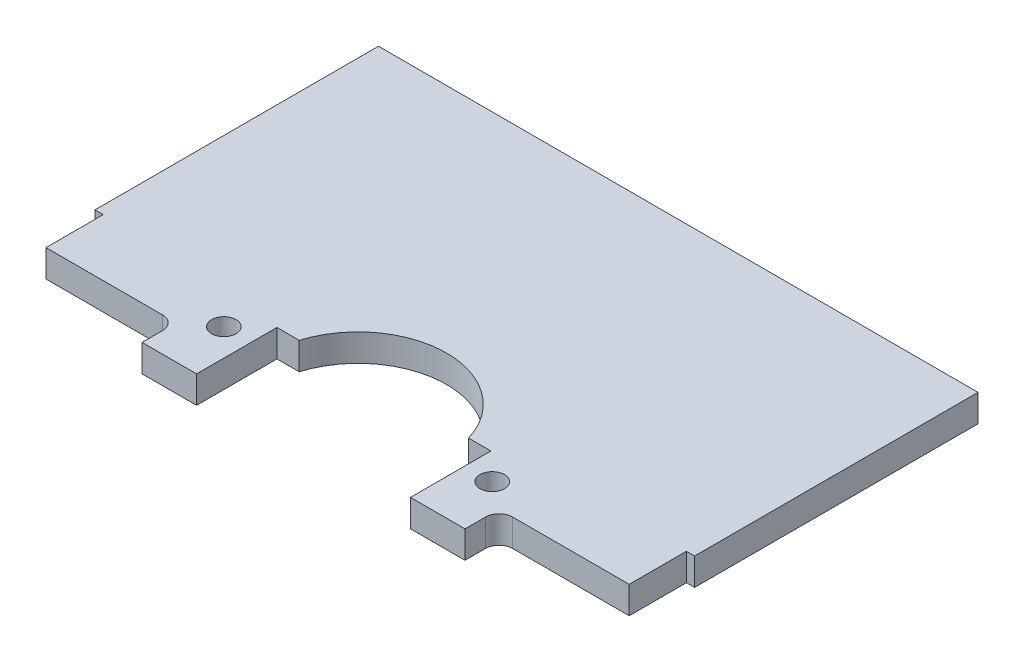
SolidWorks part; units mm, degrees
ref_plane "Front Plane" through (0, 0, 0) normal (0, 0, 1) x (1, 0, 0)
ref_plane "Top Plane" through (0, 0, 0) normal (0, 1, 0) x (1, 0, 0)
ref_plane "Right Plane" through (0, 0, 0) normal (1, 0, 0) x (0, 0, -1)
sketch "Sketch1" plane through (0, 0, 0) normal (0, 1, 0) x (1, 0, 0)
  line L0 (0, 0) -> (0, -20.1295) construction
  line L1 (-27.94, -13.208) -> (27.94, -13.208)
  line L2 (-27.94, -13.208) -> (-27.94, 13.208)
  line L3 (-27.94, 13.208) -> (27.94, 13.208)
  line L4 (27.94, -13.208) -> (27.94, 13.208)
  line L5 (-27.94, -13.208) -> (27.94, 13.208) construction
  line L6 (-27.94, 13.208) -> (27.94, -13.208) construction
  line L7 (-9.9695, -21.717) -> (-9.9695, -14.224)
  line L8 (-27.178, -18.542) -> (27.178, -18.542)
  line L9 (-27.178, -18.542) -> (-27.178, -13.208)
  line L10 (-27.178, -13.208) -> (27.178, -13.208)
  line L11 (27.178, -18.542) -> (27.178, -13.208)
  line L12 (-27.178, -18.542) -> (27.178, -13.208) construction
  line L13 (-27.178, -13.208) -> (27.178, -18.542) construction
  line L14 (-15.0495, -21.717) -> (15.0495, -21.717)
  line L15 (-15.0495, -21.717) -> (-15.0495, -18.542)
  line L16 (-15.0495, -18.542) -> (15.0495, -18.542)
  line L17 (15.0495, -21.717) -> (15.0495, -18.542)
  line L18 (-15.0495, -21.717) -> (15.0495, -18.542) construction
  line L19 (-15.0495, -18.542) -> (15.0495, -21.717) construction
  line L20 (-9.9695, -14.224) -> (9.9695, -14.224)
  line L21 (9.9695, -14.224) -> (9.9695, -21.717)
  line L22 (-12.5095, -21.717) -> (-12.5095, -16.637) construction
  line L23 (12.5095, -21.717) -> (12.5095, -16.637) construction
  line L24 (-12.5095, -16.637) -> (12.5095, -16.637) construction
  circle A0 centre (-12.5095, -16.637) radius 1.143
  circle A1 centre (12.5095, -16.637) radius 1.143
  arc A2 (-7.8945, -14.224) -> (7.8945, -14.224) centre (0, -16.637) cw
  point P0 (0, 0)
  point P8 (0, -15.875)
  dimension "D11" = 2.286
  dimension "D12" = 8.255
  dimension "D1" = 55.88
  dimension "D2" = 26.416
  dimension "D3" = 31.75
  dimension "D4" = 0.762
  dimension "D5" = 34.925
  dimension "D6" = 27.432
  dimension "D7" = 19.939
  dimension "D8" = 5.08
  dimension "D9" = 2.54
  dimension "D10" = 5.08
extrude "Boss-Extrude1" add sketch "Sketch1" along normal blind 2.54 contours L1 A2 L4 L3 L2 | L20 A2 L1 L9 L8 L7 A0 | L1 A2 L20 L21 L16 L8 L11 A1 | L15 L14 L7 L8 | L16 L21 L14 L17
fillet "Fillet1" radius 1.27 2 edges at (-15.0495, 1.27, 18.542) (15.0495, 1.27, 18.542)
sketch "hours" plane through (0, 2.54, 0) normal (0, 1, 0) x (1, 0, 0)
  line L0 (0, 0) -> (0, -16.1969) construction
  line L1 (-17.3899, 1.193) -> (-15.3064, -0.8905)
  line L2 (15.3064, -0.8905) -> (17.3899, 1.193)
  line L3 (-7.4579, 1.808) -> (-8.5432, 4.4283)
  line L4 (7.4579, 1.808) -> (8.5432, 4.4283)
  line L5 (0, 2.6059) -> (0, 5.3999)
  line L6 (-13.7582, 1.7332) -> (-12.6317, 0.2651)
  line L7 (-10.9298, 2.7341) -> (-10.0169, 1.1528)
  line L8 (-5.4082, 3.9869) -> (-4.9448, 2.2574)
  line L9 (-2.6966, 4.2856) -> (-2.4641, 2.5197)
  line L10 (2.6966, 4.2856) -> (2.4641, 2.5197)
  line L11 (5.4082, 3.9869) -> (4.9448, 2.2574)
  line L12 (10.9298, 2.7341) -> (10.0169, 1.1528)
  line L13 (13.7582, 1.7332) -> (12.6317, 0.2651)
  line L31 (-27.94, -13.208) -> (-27.178, -13.208)
  line L32 (-27.178, -13.208) -> (-27.178, -18.542)
  line L33 (-27.178, -18.542) -> (-16.3195, -18.542)
  line L34 (-15.0495, -19.812) -> (-15.0495, -21.717)
  line L35 (-15.0495, -21.717) -> (-9.9695, -21.717)
  line L36 (-9.9695, -21.717) -> (-9.9695, -14.224)
  line L37 (-9.9695, -14.224) -> (-7.8945, -14.224)
  line L38 (7.8945, -14.224) -> (9.9695, -14.224)
  line L39 (9.9695, -14.224) -> (9.9695, -21.717)
  line L40 (9.9695, -21.717) -> (15.0495, -21.717)
  line L41 (15.0495, -21.717) -> (15.0495, -19.812)
  line L42 (16.3195, -18.542) -> (27.178, -18.542)
  line L43 (27.178, -18.542) -> (27.178, -13.208)
  line L44 (27.178, -13.208) -> (27.94, -13.208)
  line L45 (27.94, -13.208) -> (27.94, 13.208)
  line L46 (27.94, 13.208) -> (-27.94, 13.208)
  line L47 (-27.94, 13.208) -> (-27.94, -13.208)
  line L48 (-27.94, -13.208) -> (-27.178, -13.208)
  line L49 (-27.178, -13.208) -> (-27.178, -18.542)
  line L50 (-27.178, -18.542) -> (-16.3195, -18.542)
  line L51 (-15.0495, -19.812) -> (-15.0495, -21.717)
  line L52 (-15.0495, -21.717) -> (-9.9695, -21.717)
  line L53 (-9.9695, -21.717) -> (-9.9695, -14.224)
  line L54 (-9.9695, -14.224) -> (-7.8945, -14.224)
  line L55 (7.8945, -14.224) -> (9.9695, -14.224)
  line L56 (9.9695, -14.224) -> (9.9695, -21.717)
  line L57 (9.9695, -21.717) -> (15.0495, -21.717)
  line L58 (15.0495, -21.717) -> (15.0495, -19.812)
  line L59 (16.3195, -18.542) -> (27.178, -18.542)
  line L60 (27.178, -18.542) -> (27.178, -13.208)
  line L61 (27.178, -13.208) -> (27.94, -13.208)
  line L62 (27.94, -13.208) -> (27.94, 13.208)
  line L63 (27.94, 13.208) -> (-27.94, 13.208)
  line L64 (-27.94, 13.208) -> (-27.94, -13.208)
  arc A0 (-14.7549, -2.0345) -> (14.7549, -2.0345) centre (0, -32.6457) cw
  arc A1 (-15.3064, -0.8905) -> (15.3064, -0.8905) centre (0, -32.6457) cw
  arc A2 (-17.3899, 1.193) -> (17.3899, 1.193) centre (0, -32.6457) cw
  arc A3 (-16.5195, 1.6264) -> (16.5195, 1.6264) centre (0, -32.6457) cw construction
  arc A4 (-16.0784, 0.7111) -> (16.0784, 0.7111) centre (0, -32.6457) cw
  circle A5 centre (-12.5095, -16.637) radius 1.143 construction
  circle A6 centre (12.5095, -16.637) radius 1.143 construction
  circle A7 centre (-12.5095, -16.637) radius 1.143
  arc A8 (-15.0495, -19.812) -> (-16.3195, -18.542) centre (-16.3195, -19.812) ccw
  arc A9 (7.8945, -14.224) -> (-7.8945, -14.224) centre (0, -16.637) ccw
  arc A10 (16.3195, -18.542) -> (15.0495, -19.812) centre (16.3195, -19.812) ccw
  arc A11 (-15.0495, -19.812) -> (-16.3195, -18.542) centre (-16.3195, -19.812) ccw
  arc A12 (7.8945, -14.224) -> (-7.8945, -14.224) centre (0, -16.637) ccw
  arc A13 (16.3195, -18.542) -> (15.0495, -19.812) centre (16.3195, -19.812) ccw
  circle A14 centre (12.5095, -16.637) radius 1.143
  dimension "D1" = 33.9816
  dimension "D3" = 16.4488
  dimension "D5" = 22.5
  dimension "D6" = 22.5
  dimension "D7" = 22.5
  dimension "D8" = 1.778
  dimension "D9" = 7.5
  dimension "D10" = 7.5
  dimension "D11" = 7.5
  dimension "D12" = 7.5
  dimension "D13" = 7.5
  dimension "D14" = 7.5
  dimension "D15" = 7.5
  dimension "D16" = 7.5
  dimension "D2" = 1.27
  dimension "D4" = 2.794
  dimension "D17" = 0
sketch "minutes" plane through (0, 0, 0) normal (0, 1, 0) x (1, 0, 0)
  line L0 (0, 0) -> (0, -16.1969) construction
  line L1 (-17.3899, 1.193) -> (-15.3064, -0.8905)
  line L2 (15.3064, -0.8905) -> (17.3899, 1.193)
  line L3 (-4.9448, 2.2574) -> (-5.6729, 4.9746)
  line L4 (-8.1488, 3.4762) -> (-7.4579, 1.808)
  line L5 (0, 2.6059) -> (0, 5.3999)
  line L6 (-13.7582, 1.7332) -> (-12.6317, 0.2651)
  line L7 (-11.4505, 3.6359) -> (-10.0169, 1.1528)
  line L8 (2.6966, 4.2856) -> (2.4641, 2.5197)
  line L9 (-2.6966, 4.2856) -> (-2.4641, 2.5197)
  line L10 (4.9448, 2.2574) -> (5.6729, 4.9746)
  line L11 (8.1488, 3.4762) -> (7.4579, 1.808)
  line L12 (11.4505, 3.6359) -> (10.0169, 1.1528)
  line L13 (13.7582, 1.7332) -> (12.6317, 0.2651)
  line L14 (17.3899, 1.193) -> (15.3064, -0.8905)
  line L48 (-27.94, -13.208) -> (-27.178, -13.208)
  line L49 (-27.178, -13.208) -> (-27.178, -18.542)
  line L50 (-27.178, -18.542) -> (-16.3195, -18.542)
  line L51 (-15.0495, -19.812) -> (-15.0495, -21.717)
  line L52 (-15.0495, -21.717) -> (-9.9695, -21.717)
  line L53 (-9.9695, -21.717) -> (-9.9695, -14.224)
  line L54 (-9.9695, -14.224) -> (-7.8945, -14.224)
  line L55 (7.8945, -14.224) -> (9.9695, -14.224)
  line L56 (9.9695, -14.224) -> (9.9695, -21.717)
  line L57 (9.9695, -21.717) -> (15.0495, -21.717)
  line L58 (15.0495, -21.717) -> (15.0495, -19.812)
  line L59 (16.3195, -18.542) -> (27.178, -18.542)
  line L60 (27.178, -18.542) -> (27.178, -13.208)
  line L61 (27.178, -13.208) -> (27.94, -13.208)
  line L62 (27.94, -13.208) -> (27.94, 13.208)
  line L63 (27.94, 13.208) -> (-27.94, 13.208)
  line L64 (-27.94, 13.208) -> (-27.94, -13.208)
  arc A0 (-14.7549, -2.0345) -> (14.7549, -2.0345) centre (0, -32.6457) cw
  arc A1 (-15.3064, -0.8905) -> (15.3064, -0.8905) centre (0, -32.6457) cw
  arc A2 (-17.3899, 1.193) -> (17.3899, 1.193) centre (0, -32.6457) cw
  arc A3 (-16.5195, 1.6264) -> (16.5195, 1.6264) centre (0, -32.6457) cw construction
  arc A4 (-16.6343, 0.4374) -> (16.6343, 0.4374) centre (0, -32.6457) cw
  arc A5 (-16.0784, 0.7111) -> (16.0784, 0.7111) centre (0, -32.6457) cw construction
  circle A6 centre (-12.5095, -16.637) radius 1.143 construction
  circle A7 centre (-12.5095, -16.637) radius 1.143
  circle A8 centre (12.5095, -16.637) radius 1.143 construction
  arc A11 (-15.0495, -19.812) -> (-16.3195, -18.542) centre (-16.3195, -19.812) ccw
  arc A12 (7.8945, -14.224) -> (-7.8945, -14.224) centre (0, -16.637) ccw
  arc A13 (16.3195, -18.542) -> (15.0495, -19.812) centre (16.3195, -19.812) ccw
  circle A14 centre (12.5095, -16.637) radius 1.143
  dimension "D1" = 33.9816
  dimension "D3" = 16.4488
  dimension "D5" = 15
  dimension "D6" = 15
  dimension "D7" = 15
  dimension "D8" = 1.778
  dimension "D9" = 7.5
  dimension "D10" = 7.5
  dimension "D11" = 7.5
  dimension "D2" = 1.27
  dimension "D4" = 2.794
